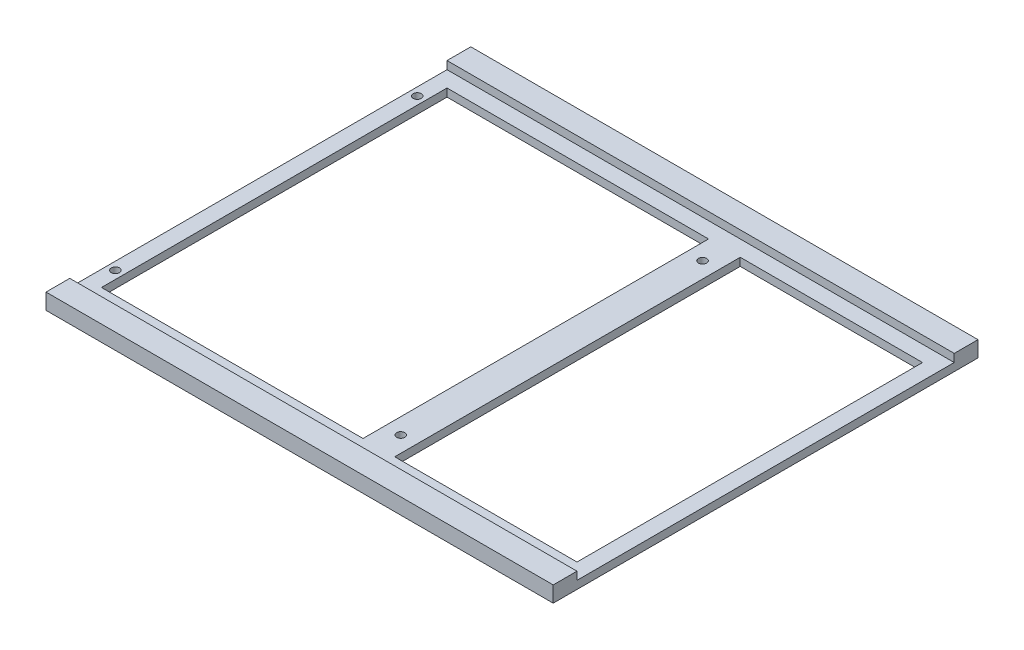
SolidWorks part; units mm, degrees
ref_plane "Front Plane" through (0, 0, 0) normal (0, 0, 1) x (1, 0, 0)
ref_plane "Top Plane" through (0, 0, 0) normal (0, 1, 0) x (1, 0, 0)
ref_plane "Right Plane" through (0, 0, 0) normal (1, 0, 0) x (0, 0, -1)
sketch "Sketch1" plane through (0, 0, 0) normal (0, 1, 0) x (1, 0, 0)
  line L1 (101.6, -85.09) -> (-101.6, -85.09)
  line L2 (101.6, -85.09) -> (101.6, 85.09)
  line L3 (101.6, 85.09) -> (-101.6, 85.09)
  line L4 (-101.6, -85.09) -> (-101.6, 85.09)
  line L5 (101.6, -85.09) -> (-101.6, 85.09) construction
  line L6 (101.6, 85.09) -> (-101.6, -85.09) construction
  point P0 (0, 0)
  dimension "D1" = 203.2
  dimension "D2" = 170.18
extrude "Boss-Extrude1" add sketch "Sketch1" along normal blind 6.35
sketch "Sketch3" plane through (101.6, 0, 0) normal (1, 0, 0) x (0, 0, -1)
  line L0 (-85.09, 6.35) -> (85.09, 6.35) construction
  line L1 (75.565, 3.175) -> (-75.565, 3.175)
  line L2 (75.565, 3.175) -> (75.565, 6.35)
  line L3 (75.565, 6.35) -> (-75.565, 6.35)
  line L4 (-75.565, 3.175) -> (-75.565, 6.35)
  line L5 (75.565, 3.175) -> (-75.565, 6.35) construction
  line L6 (75.565, 6.35) -> (-75.565, 3.175) construction
  line L7 (-85.09, 0) -> (85.09, 0) construction
  line L8 (-85.09, 6.35) -> (-85.09, 0) construction
  point P0 (0, 4.7625)
  point P10 (0, 0)
  dimension "D1" = 9.525
  dimension "D2" = 3.175
extrude "Cut-Extrude1" cut sketch "Sketch3" against normal through all
sketch "Sketch4" plane through (0, 3.175, 0) normal (0, 1, 0) x (1, 0, 0)
  line L1 (-101.6, -75.565) -> (-101.6, 75.565) construction
  line L2 (95.25, -69.215) -> (-95.25, -69.215)
  line L3 (95.25, -69.215) -> (95.25, 69.215)
  line L4 (95.25, 69.215) -> (-95.25, 69.215)
  line L5 (-95.25, -69.215) -> (-95.25, 69.215)
  line L6 (95.25, -69.215) -> (-95.25, 69.215) construction
  line L7 (95.25, 69.215) -> (-95.25, -69.215) construction
  line L8 (-101.6, 75.565) -> (101.6, 75.565) construction
  line L9 (22.225, -69.215) -> (22.225, 69.215)
  line L10 (9.525, -69.215) -> (9.525, 69.215)
  line L11 (-101.6, -11.9685) -> (-95.25, -11.9685) construction
  line L12 (9.525, 38.4482) -> (22.225, 38.4482) construction
  line L13 (15.875, 38.4482) -> (15.875, -96.3543) construction
  line L14 (-98.425, -11.9685) -> (-98.425, 16.517) construction
  point P0 (0, 0)
  dimension "D1" = 6.35
  dimension "D2" = 6.35
  dimension "D3" = 12.7
  dimension "D4" = 114.3
extrude "Cut-Extrude3" cut sketch "Sketch4" against normal through all contours L2 L10 L4 L5 | L9 L2 L3 L4
hole_wizard "M4x0.7 Tapped Hole1" positions "Sketch6" profile "Sketch5" tap size "M4x0.7" standard "ANSI Metric"
sketch "Sketch6" plane through (0, 3.175, 0) normal (0, 1, 0) x (1, 0, 0)
  line L0 (-98.425, -60.452) -> (-98.425, 60.452) construction
  line L2 (-95.25, -65.1111) -> (-101.6, -65.1111) construction
  line L3 (-95.25, -69.215) -> (-95.25, 69.215) construction
  line L4 (-101.6, -75.565) -> (-101.6, 75.565) construction
  line L5 (15.875, 60.452) -> (15.875, -60.452) construction
  line L7 (9.525, 0) -> (22.225, 0) construction
  line L8 (9.525, -69.215) -> (9.525, 69.215) construction
  line L9 (22.225, -69.215) -> (22.225, 69.215) construction
  point P0 (-98.425, -60.452)
  point P2 (-98.425, 60.452)
  point P9 (-98.425, 0)
  point P19 (-98.425, -65.1111)
  point P20 (15.875, 60.452)
  point P22 (15.875, -60.452)
  point P37 (15.875, 0)
  dimension "D1" = 120.904
sketch "Sketch5" plane through (-98.425, 3.175, 60.452) normal (1, 0, 0) x (0, 0, 1)
  line L0 (0, 0) -> (0, 9.906)
  line L1 (0, 9.906) -> (1.65, 9.906)
  line L2 (1.65, 9.906) -> (1.65, 0)
  line L5 (1.65, 0) -> (0, 0)
  line L10 (0, 9.906) -> (-1.65, 9.906) construction
  line L11 (0, -6.35) -> (0, 107.95) construction
  dimension "Tap Drill Dia." = 3.3
  dimension "Tap Drill Depth" = 9.906
  dimension "Drill Angle" = 180
cosmetic thread "Hole Thread1" parameters "D1"=3.175, "D2"=4
cosmetic thread "Hole Thread2" parameters "D1"=3.175, "D2"=4
cosmetic thread "Hole Thread3" parameters "D1"=3.175, "D2"=4
cosmetic thread "Hole Thread4" parameters "D1"=3.175, "D2"=4
